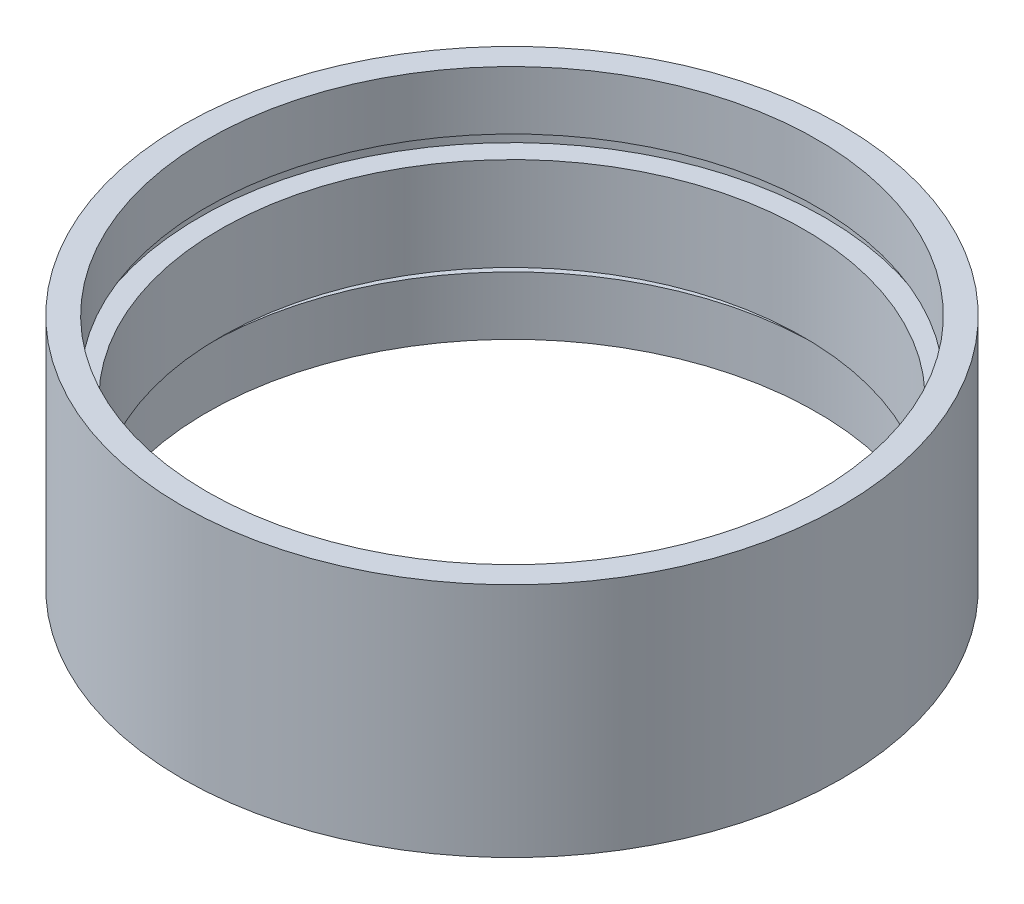
SolidWorks part; units mm, degrees
ref_plane "前视基准面" through (0, 0, 0) normal (0, 0, 1) x (1, 0, 0)
ref_plane "上视基准面" through (0, 0, 0) normal (0, 1, 0) x (1, 0, 0)
ref_plane "右视基准面" through (0, 0, 0) normal (1, 0, 0) x (0, 0, -1)
sketch "草图1" plane through (0, 0, 0) normal (0, 0, 1) x (1, 0, 0)
  line L0 (0, 161.3762) -> (0, 0) construction
  line L1 (141.7365, 0) -> (-131.7984, 0) construction
  line L2 (25.4, 0) -> (25.4, 18.2)
  line L3 (23.5, 0) -> (23.5, 4.5)
  line L4 (24.1, 4.5) -> (24.1, 5.5)
  line L5 (22.5, 5.5) -> (22.5, 12.7)
  line L6 (22.5, 5.5) -> (24.1, 5.5)
  line L7 (24.1, 12.7) -> (24.1, 13.7)
  line L8 (22.5, 12.7) -> (24.1, 12.7)
  line L9 (23.5, 13.7) -> (23.5, 18.2)
  line L10 (24.1, 13.7) -> (23.5, 13.7)
  line L11 (23.5, 18.2) -> (25.4, 18.2)
  line L12 (23.5, 0) -> (25.4, 0)
  line L13 (23.5, 4.5) -> (24.1, 4.5)
  dimension "D1" = 25.4
  dimension "D2" = 23.5
  dimension "D3" = 4.5
  dimension "D4" = 24.1
  dimension "D5" = 22.5
  dimension "D6" = 24.1
  dimension "D7" = 1
  dimension "D8" = 5.5
  dimension "D9" = 12.7
  dimension "D10" = 1
revolve "旋转1" add sketch "草图1" angle 360 about L0
cosmetic thread "装饰螺纹线1" parameters "D2"=48
cosmetic thread "装饰螺纹线2" parameters "D2"=46
cosmetic thread "装饰螺纹线3" parameters "D2"=48
